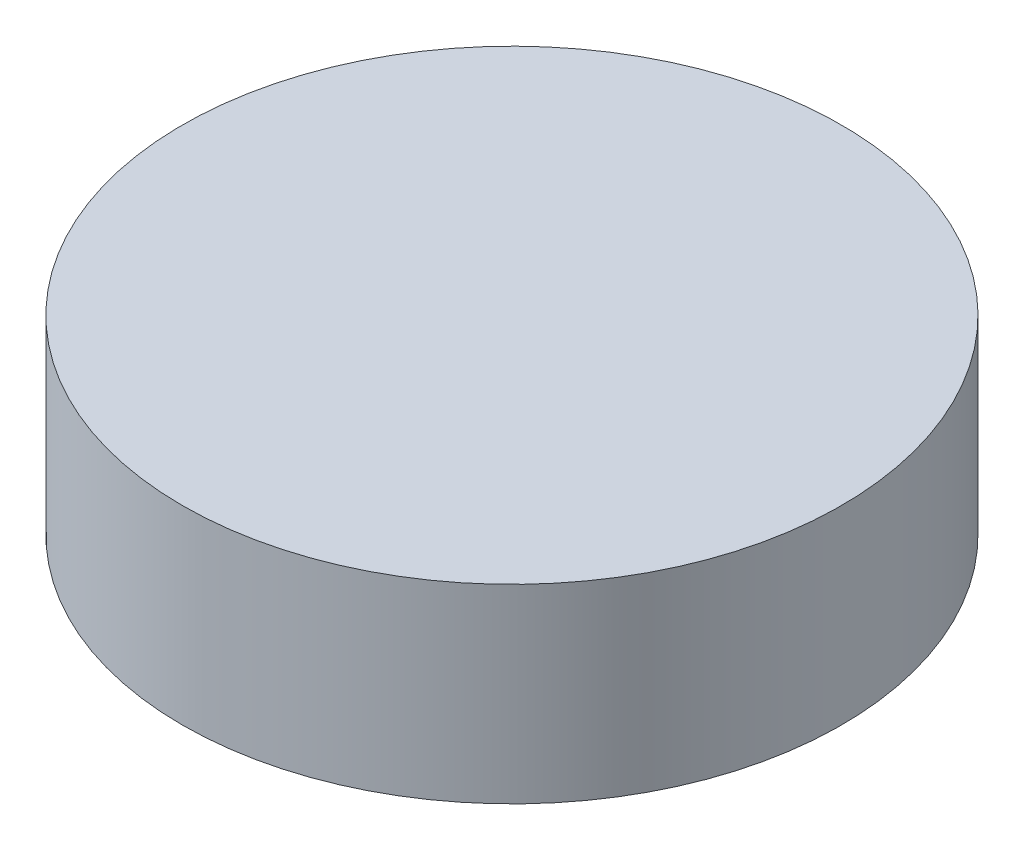
SolidWorks part; units mm, degrees
material "Glass"
ref_plane "Front Plane" through (0, 0, 0) normal (0, 0, 1) x (1, 0, 0)
ref_plane "Top Plane" through (0, 0, 0) normal (0, 1, 0) x (1, 0, 0)
ref_plane "Right Plane" through (0, 0, 0) normal (1, 0, 0) x (0, 0, -1)
sketch "Sketch1" plane through (0, 0, 0) normal (0, 1, 0) x (1, 0, 0)
  circle A0 centre (0, 0) radius 13
extrude "Boss-Extrude1" add sketch "Sketch1" along normal blind 7.5
